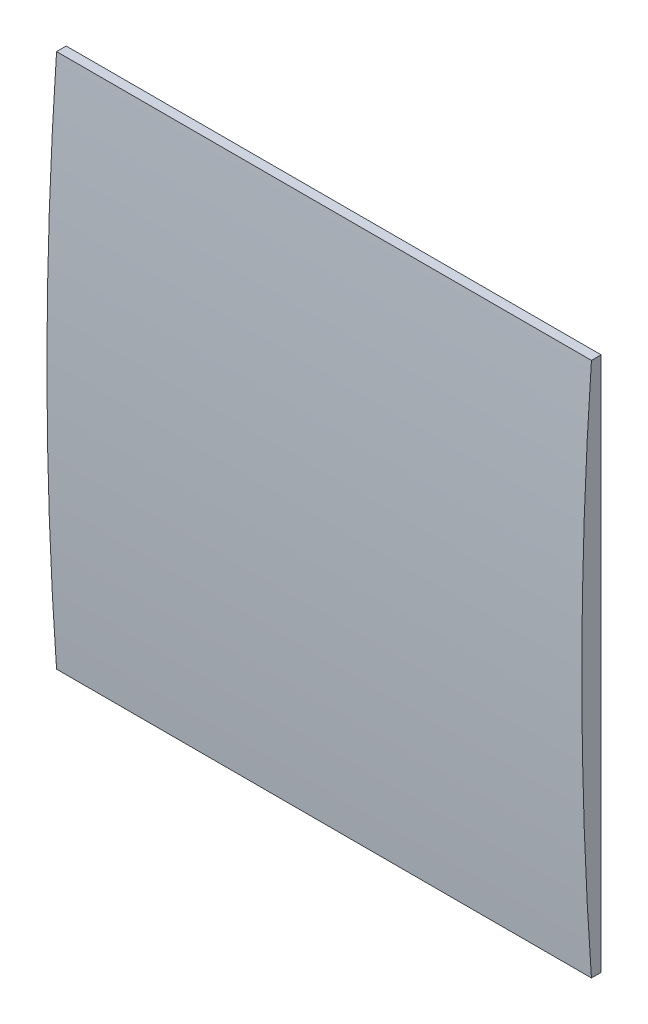
SolidWorks part; units mm, degrees
ref_plane "Front Plane" through (0, 0, 0) normal (0, 0, 1) x (1, 0, 0)
ref_plane "Top Plane" through (0, 0, 0) normal (0, 1, 0) x (1, 0, 0)
ref_plane "Right Plane" through (0, 0, 0) normal (1, 0, 0) x (0, 0, -1)
sketch "Sketch17" plane through (0, 0, 0) normal (0, 0, 1) x (1, 0, 0)
  line L1 (0, 27.7) -> (27.7, 27.7)
  line L2 (0, 27.7) -> (0, 0)
  line L3 (0, 0) -> (27.7, 0)
  line L4 (27.7, 27.7) -> (27.7, 0)
sketch "Sketch14" plane through (0, 0, 0) normal (1, 0, 0) x (0, 0, -1)
  line L0 (-2.5, 0) -> (-3.5, 0) construction
  line L3 (-3.5, 0) -> (-3.5, 27.7) construction
  line L4 (-3.5, 27.7) -> (-2.5, 27.7) construction
  line L5 (-2.5, 27.7) -> (-2.5, 0)
  line L6 (-3.5, 13.85) -> (-2.5, 13.85) construction
  line L7 (-3, 27.7) -> (-2.5, 27.7)
  line L8 (-3, 0) -> (-2.5, 0)
  arc A0 (-3.5, 13.85) -> (-3, 0) centre (188.5725, 13.85) ccw
  arc A2 (-3.5, 13.85) -> (-3, 27.7) centre (188.5725, 13.85) cw
extrude "Boss-Extrude7" add sketch "Sketch14" along normal up to vertex (27.7 mm away) up to point (27.7, 27.7, 0)
